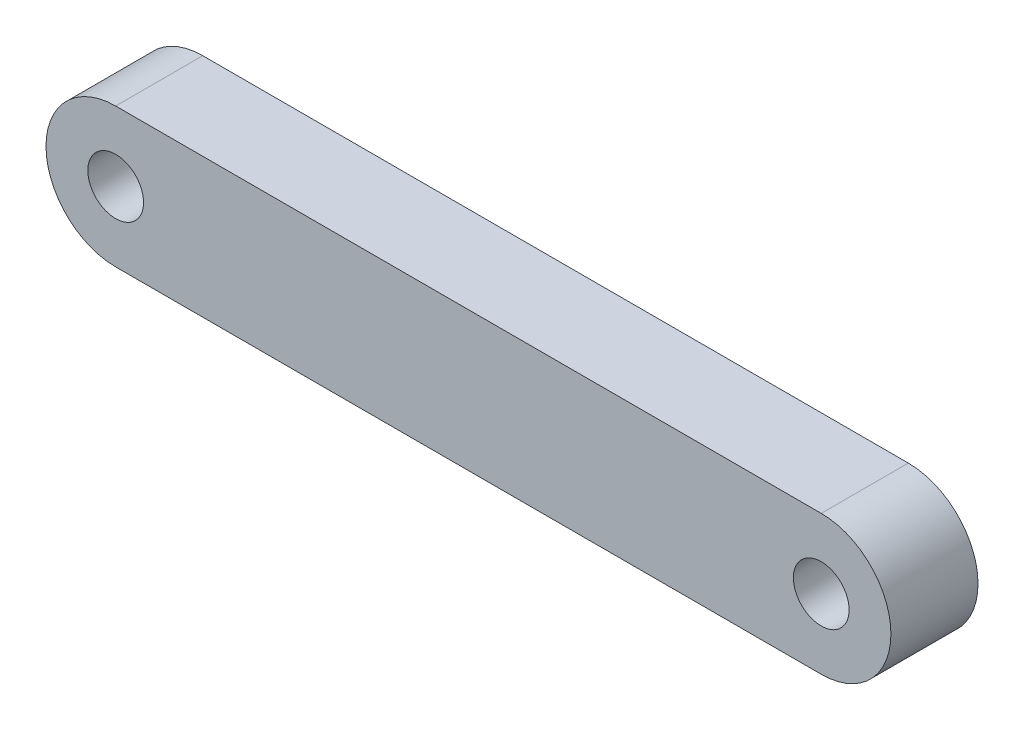
SolidWorks part; units mm, degrees
ref_plane "Plan de face" through (0, 0, 0) normal (0, 0, 1) x (1, 0, 0)
ref_plane "Plan de dessus" through (0, 0, 0) normal (0, 1, 0) x (1, 0, 0)
ref_plane "Plan de droite" through (0, 0, 0) normal (1, 0, 0) x (0, 0, -1)
sketch "Esquisse1" plane through (0, 0, 0) normal (0, 0, 1) x (1, 0, 0)
  line L0 (-4.2884, 4) -> (52.6919, 4) construction
  line L1 (4, 0) -> (44.5, 0)
  line L3 (4, 8) -> (44.5, 8)
  circle A0 centre (4, 4) radius 1.6
  circle A1 centre (44.5, 4) radius 1.6
  arc A3 (4, 8) -> (4, 0) centre (4, 4) ccw
  arc A4 (44.5, 0) -> (44.5, 8) centre (44.5, 4) ccw
  dimension "D3" = 40.5
  dimension "D5" = 4
  dimension "D6" = 4
extrude "Boss.-Extru.1" add sketch "Esquisse1" along normal blind 5 contours L1 A4 L3 A3
sketch "Esquisse3" plane through (0, 0, 0) normal (0, 0, 1) x (1, 0, 0)
  circle A0 centre (4, 4) radius 1.6
  circle A1 centre (44.5, 4) radius 1.6
extrude "Enlèv. mat.-Extru.2" cut sketch "Esquisse3" along normal through all
